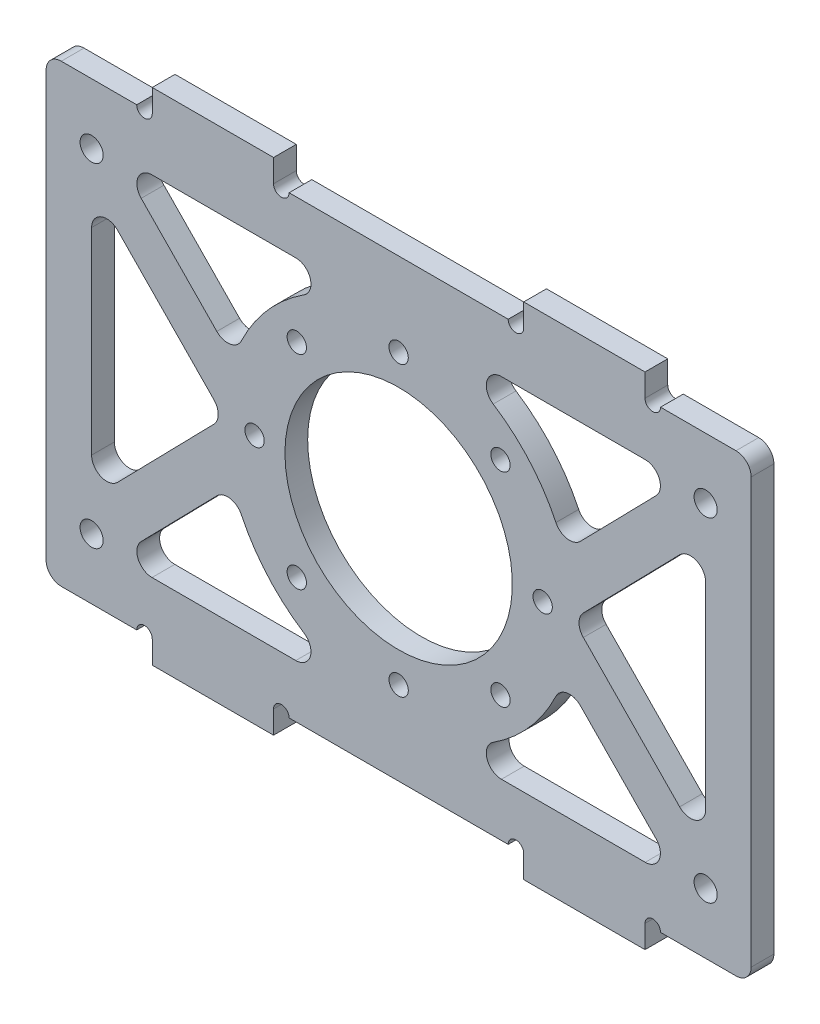
SolidWorks part; units mm, degrees
material "Thornel Mat VMA"
ref_plane "前视基准面" through (0, 0, 0) normal (0, 0, 1) x (1, 0, 0)
ref_plane "上视基准面" through (0, 0, 0) normal (0, 1, 0) x (1, 0, 0)
ref_plane "右视基准面" through (0, 0, 0) normal (1, 0, 0) x (0, 0, -1)
sketch "草图1" plane through (0, 0, 0) normal (0, 0, 1) x (1, 0, 0)
  line L1 (-46.5, -30) -> (46.5, -30)
  line L2 (-46.5, -30) -> (-46.5, 30)
  line L3 (-46.5, 30) -> (46.5, 30)
  line L4 (46.5, -30) -> (46.5, 30)
  line L5 (0, 30) -> (0, -30) construction
  line L6 (-46.5, 0) -> (46.5, 0) construction
  point P0 (0, 0)
  dimension "D1" = 60
  dimension "D2" = 93
extrude "凸台-拉伸1" add sketch "草图1" along normal mid plane 3
sketch "草图2" plane through (0, 0, 1.5) normal (0, 0, 1) x (1, 0, 0)
  circle A0 centre (0, 0) radius 15
  dimension "D1" = 30
extrude "切除-拉伸1" cut sketch "草图2" against normal mid plane 24
sketch "草图3" plane through (0, 0, 1.5) normal (0, 0, 1) x (1, 0, 0)
  line L0 (0, 24.5) -> (0, 0) construction
  line L1 (0, 0) -> (21.2176, 12.25) construction
  circle A0 centre (0, 0) radius 24.5 construction
  circle A1 centre (21.2176, 12.25) radius 1.275
  circle A2 centre (21.2176, -12.25) radius 1.275
  circle A3 centre (0, -24.5) radius 1.275
  circle A4 centre (-21.2176, -12.25) radius 1.275
  circle A5 centre (-21.2176, 12.25) radius 1.275
  circle A6 centre (0, 24.5) radius 1.275
  point P17 (0, 0)
  dimension "D1" = 49
  dimension "D2" = 2.55
  dimension "D4" = 60
  dimension "D3" = 6
extrude "切除-拉伸2" [suppressed] cut sketch "草图3" against normal mid plane 24
sketch "草图4" plane through (0, 0, 1.5) normal (0, 0, 1) x (1, 0, 0)
  line L0 (40.5, -22) -> (40.5, 22) construction
  line L1 (0, 0) -> (40.5, 0) construction
  line L2 (46.5, -30) -> (46.5, 30) construction
  line L3 (46.5, 30) -> (-46.5, 30) construction
  line L4 (0, 0) -> (0, 37.3634) construction
  circle A0 centre (40.5, -22) radius 1.525
  circle A1 centre (40.5, 22) radius 1.525
  circle A2 centre (-40.5, -22) radius 1.525
  circle A3 centre (-40.5, 22) radius 1.525
  point P3 (40.5, 0)
  dimension "D3" = 3.05
  dimension "D1" = 6
  dimension "D2" = 8
extrude "切除-拉伸3" cut sketch "草图4" against normal mid plane 30
sketch "草图5" plane through (0, 0, 1.5) normal (0, 0, 1) x (1, 0, 0)
  circle A0 centre (0, 0) radius 19 construction
  circle A1 centre (0, 19) radius 1.275
  circle A2 centre (13.435, 13.435) radius 1.275
  circle A3 centre (19, 0) radius 1.275
  circle A4 centre (13.435, -13.435) radius 1.275
  circle A5 centre (0, -19) radius 1.275
  circle A6 centre (-13.435, -13.435) radius 1.275
  circle A7 centre (-19, 0) radius 1.275
  circle A8 centre (-13.435, 13.435) radius 1.275
  point P21 (0, 0)
  dimension "D1" = 38
  dimension "D2" = 2.55
  dimension "D3" = 8
extrude "切除-拉伸4" cut sketch "草图5" against normal mid plane 30
sketch "草图6" [suppressed] plane through (0, 0, 1.5) normal (0, 0, 1) x (1, 0, 0)
  line L0 (21.2176, 12.25) -> (40.5, 22) construction
  line L1 (26.3558, 11.4864) -> (41.5, 19.1439)
  line L2 (41.5, 19.1439) -> (41.5, -19.1439)
  line L3 (41.5, -19.1439) -> (26.3558, -11.4864)
  line L4 (0, 0) -> (41.5, 0) construction
  line L5 (46.5, -30) -> (46.5, 30) construction
  arc A0 (26.3558, -11.4864) -> (26.3558, 11.4864) centre (0, 0) ccw
  circle A1 centre (0, 0) radius 21.75 construction
  dimension "D1" = 7
  dimension "D2" = 3
  dimension "D3" = 5
extrude "切除-拉伸5" [suppressed] cut sketch "草图6" against normal blind 10
mirror "镜向1" [suppressed] about plane through (0, 0, 0) normal (1, 0, 0)
fillet "圆角1" [suppressed] radius 2
sketch "草图8" [suppressed] plane through (0, 0, 1.5) normal (0, 0, 1) x (1, 0, 0)
  line L0 (14.1973, 25) -> (39.7847, 25)
  line L1 (39.7847, 25) -> (23.3938, 16.7121)
  line L2 (38.5975, 17.6763) -> (27.9893, 12.3123) construction
  line L3 (44.5, 30) -> (-44.5, 30) construction
  line L4 (0, 0) -> (62.8695, 0) construction
  line L5 (39.7847, -25) -> (23.3938, -16.7121)
  line L6 (14.1973, -25) -> (39.7847, -25)
  arc A0 (23.3938, 16.7121) -> (14.1973, 25) centre (0, 0) ccw
  arc A1 (27.0126, -9.8428) -> (27.0126, 9.8428) centre (0, 0) ccw construction
  arc A2 (23.3938, -16.7121) -> (14.1973, -25) centre (0, 0) cw
  dimension "D1" = 6
  dimension "D2" = 5
extrude "切除-拉伸6" [suppressed] cut sketch "草图8" against normal blind 10
mirror "镜向2" [suppressed] about plane through (0, 0, 0) normal (1, 0, 0)
fillet "圆角2" [suppressed] radius 2
sketch "草图9" plane through (0, 0, 1.5) normal (0, 0, 1) x (1, 0, 0)
  line L0 (40.5, 22) -> (19, 0) construction
  line L1 (19, 0) -> (40.5, -22) construction
  line L2 (40.5, 17.907) -> (23, 0)
  line L3 (23, 0) -> (40.5, -17.907)
  line L4 (40.5, 17.907) -> (40.5, -17.907)
  line L5 (46.5, -30) -> (46.5, 30) construction
  line L6 (0, 0) -> (0, -19) construction
  line L7 (-40.5, 17.907) -> (-23, 0) construction
  line L8 (-23, 0) -> (-40.5, -17.907) construction
  line L9 (-40.5, 17.907) -> (-40.5, -17.907) construction
  line L10 (0, 30) -> (0, 15) construction
  line L11 (46.5, 30) -> (-46.5, 30) construction
  line L12 (37.2826, 23) -> (21.8434, 7.2018)
  line L13 (37.2826, 23) -> (0, 23)
  line L14 (0, 0) -> (15, 0) construction
  line L15 (37.2826, -23) -> (0, -23)
  line L16 (37.2826, -23) -> (21.8434, -7.2018)
  circle A1 centre (0, 0) radius 15 construction
  arc A2 (21.8434, 7.2018) -> (0, 23) centre (0, 0) ccw
  arc A3 (21.8434, -7.2018) -> (0, -23) centre (0, 0) cw
  dimension "D1" = 23
  dimension "D2" = 6
  dimension "D3" = 3
  dimension "D4" = 2.8607
extrude "切除-拉伸7" cut sketch "草图9" against normal blind 10
fillet "圆角3" radius 2 9 edges at (40.5, -17.907, 0) (23, 0, 0) (40.5, 17.907, 0) (37.2826, 23, 0) (21.8434, 7.2018, 0) (0, 23, 0) (0, -23, 0) (37.2826, -23, 0) (21.8434, -7.2018, 0)
mirror "镜向3" about plane through (0, 0, 0) normal (1, 0, 0) of "切除-拉伸7", "圆角3"
fillet "圆角4" radius 2 4 edges at (-46.5, 30, 0) (46.5, 30, 0) (46.5, -30, 0) (-46.5, -30, 0)
sketch "草图10" plane through (0, 0, -1.5) normal (0, 0, -1) x (-1, 0, 0)
  line L0 (-44.5, 30) -> (44.5, 30) construction
  line L1 (-32.5, 27) -> (-16.5, 27)
  line L2 (-32.5, 27) -> (-32.5, 33)
  line L3 (-32.5, 33) -> (-16.5, 33)
  line L4 (-16.5, 27) -> (-16.5, 33)
  line L5 (-32.5, 27) -> (-16.5, 33) construction
  line L6 (-32.5, 33) -> (-16.5, 27) construction
  line L7 (-46.5, -28) -> (-46.5, 28) construction
  point P0 (-24.5, 30)
  dimension "D1" = 3
  dimension "D2" = 14
  dimension "D3" = 16
extrude "凸台-拉伸2" add sketch "草图10" against normal up to surface (3 mm away) up to face at (-22.9221, 17.4749, 1.5)
mirror "镜向4" about plane through (0, 0, 0) normal (1, 0, 0) of "凸台-拉伸2"
mirror "镜向5" about plane through (0, 0, 0) normal (0, 1, 0) of "镜向4", "凸台-拉伸2"
sketch "草图11" plane through (0, 0, 1.5) normal (0, 0, 1) x (1, 0, 0)
  line L0 (44.5, 30) -> (32.5, 30) construction
  line L1 (16.5, 30) -> (-16.5, 30) construction
  line L2 (-32.5, 30) -> (-44.5, 30) construction
  line L3 (-44.5, -30) -> (-32.5, -30) construction
  line L4 (-16.5, -30) -> (16.5, -30) construction
  line L5 (32.5, -30) -> (44.5, -30) construction
  circle A0 centre (33.525, 30) radius 1.025
  circle A1 centre (15.475, 30) radius 1.025
  circle A2 centre (-15.475, 30) radius 1.025
  circle A3 centre (-33.525, 30) radius 1.025
  circle A4 centre (-33.525, -30) radius 1.025
  circle A5 centre (-15.475, -30) radius 1.025
  circle A6 centre (15.475, -30) radius 1.025
  circle A7 centre (33.525, -30) radius 1.025
  dimension "D1" = 2.05
extrude "切除-拉伸8" cut sketch "草图11" against normal up to surface (3 mm away) up to face at (0, 0, -1.5)
